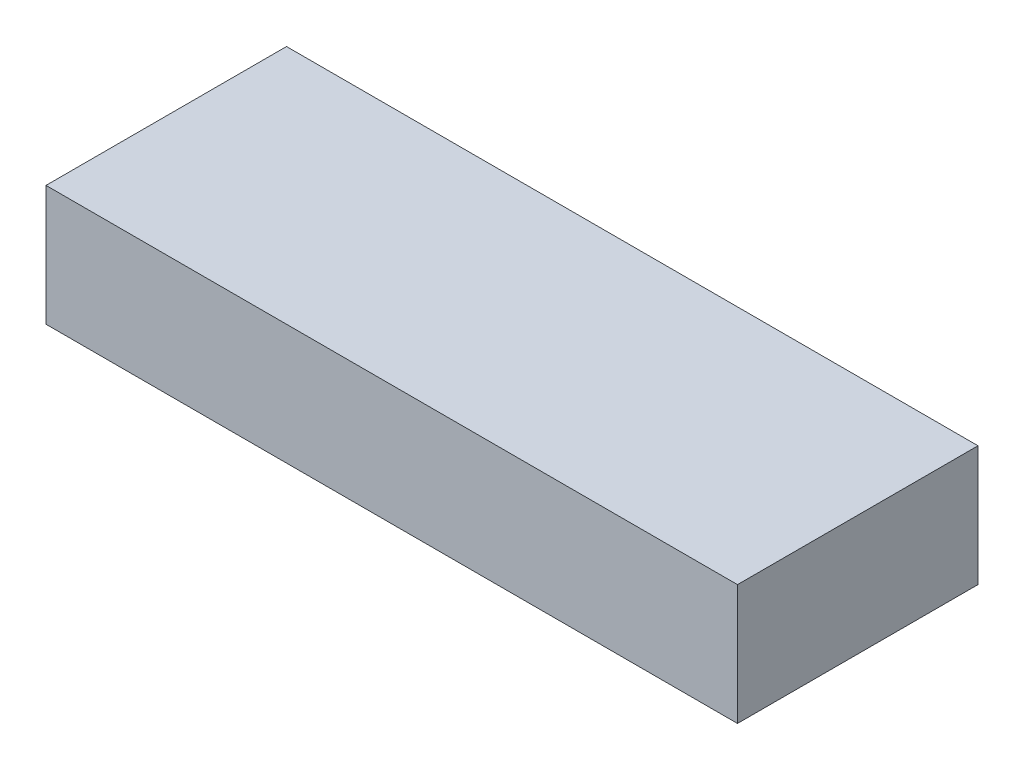
SolidWorks part; units mm, degrees
ref_plane "Front Plane" through (0, 0, 0) normal (0, 0, 1) x (1, 0, 0)
ref_plane "Top Plane" through (0, 0, 0) normal (0, 1, 0) x (1, 0, 0)
ref_plane "Right Plane" through (0, 0, 0) normal (1, 0, 0) x (0, 0, -1)
sketch "Sketch1" plane through (0, 0, 0) normal (0, 1, 0) x (1, 0, 0)
  line L1 (0, 25.4) -> (146.05, 25.4)
  line L2 (0, 25.4) -> (0, -25.4)
  line L3 (0, -25.4) -> (146.05, -25.4)
  line L4 (146.05, 25.4) -> (146.05, -25.4)
  point P4 (0, 0)
  dimension "D1" = 146.05
  dimension "D2" = 50.8
extrude "Boss-Extrude1" add sketch "Sketch1" along normal blind 25.4
